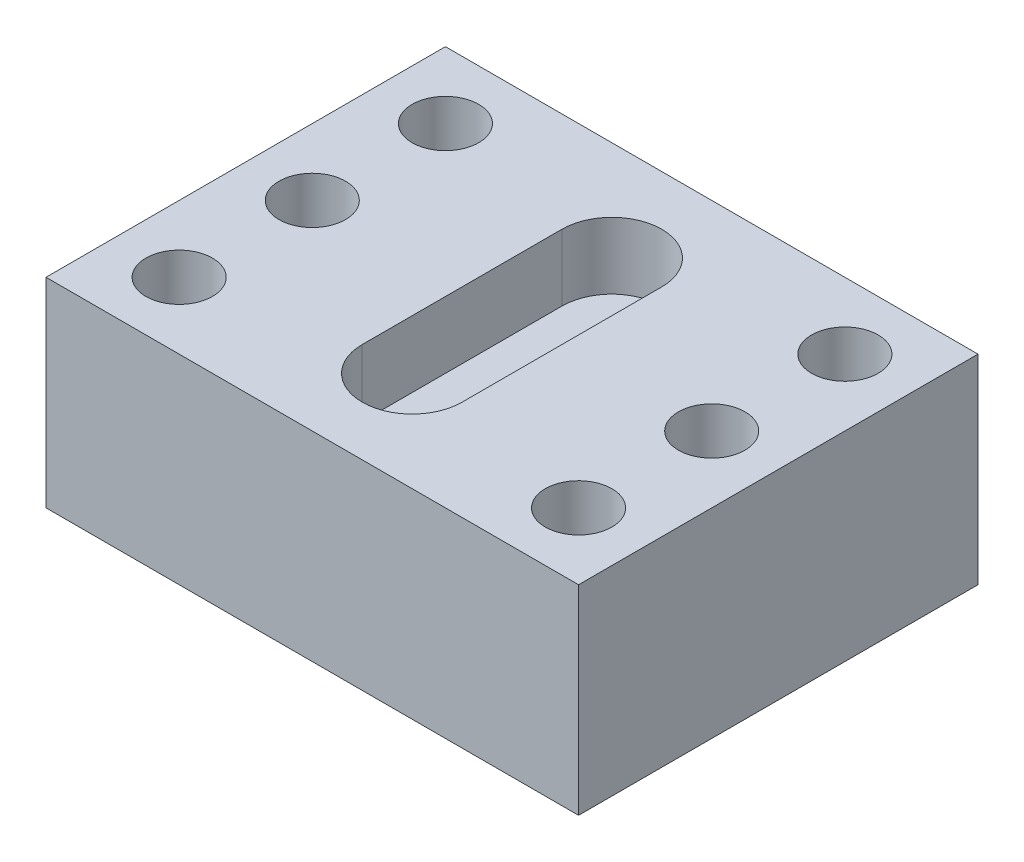
SolidWorks part; units mm, degrees
material "Plain Carbon Steel"
ref_plane "Front Plane" through (0, 0, 0) normal (0, 0, 1) x (1, 0, 0)
ref_plane "Top Plane" through (0, 0, 0) normal (0, 1, 0) x (1, 0, 0)
ref_plane "Right Plane" through (0, 0, 0) normal (1, 0, 0) x (0, 0, -1)
sketch "Sketch1" plane through (0, 0, 0) normal (0, 1, 0) x (1, 0, 0)
  line L1 (-101.6, -76.2) -> (101.6, -76.2)
  line L2 (-101.6, -76.2) -> (-101.6, 76.2)
  line L3 (-101.6, 76.2) -> (101.6, 76.2)
  line L4 (101.6, -76.2) -> (101.6, 76.2)
  line L5 (-101.6, -76.2) -> (101.6, 76.2) construction
  line L6 (-101.6, 76.2) -> (101.6, -76.2) construction
  point P0 (0, 0)
  dimension "D1" = 152.4
  dimension "D2" = 203.2
extrude "Boss-Extrude1" add sketch "Sketch1" along normal blind 76.2
sketch "Sketch2" plane through (0, 76.2, 0) normal (0, 1, 0) x (1, 0, 0)
  line L0 (-101.6, 76.2) -> (-101.6, -76.2) construction
  line L1 (-101.6, -76.2) -> (101.6, -76.2) construction
  line L2 (101.6, 76.2) -> (-101.6, 76.2) construction
  line L3 (0, 76.2) -> (0, -76.2) construction
  line L4 (-101.6, 0) -> (101.6, 0) construction
  line L6 (101.6, -76.2) -> (101.6, 76.2) construction
  line L9 (-19.05, -38.1) -> (-19.05, 38.1)
  line L11 (19.05, -38.1) -> (19.05, 38.1)
  circle A0 centre (-76.2, -50.8) radius 12.7
  circle A1 centre (-76.2, 0) radius 12.7
  circle A2 centre (-76.2, 50.8) radius 12.7
  circle A3 centre (76.2, 50.8) radius 12.7
  circle A4 centre (76.2, -50.8) radius 12.7
  circle A5 centre (76.2, 0) radius 12.7
  arc A6 (-19.05, -38.1) -> (19.05, -38.1) centre (0, -38.1) ccw
  arc A7 (-19.05, 38.1) -> (19.05, 38.1) centre (0, 38.1) cw
  point P23 (0, 0)
  dimension "D1" = 25.4
  dimension "D8" = 38.1
  dimension "D2" = 25.4
  dimension "D3" = 25.4
  dimension "D4" = 50.8
  dimension "D5" = 50.8
  dimension "D6" = 25.4
  dimension "D7" = 76.2
  dimension "D9" = 38.1
  dimension "D10" = 101.6
extrude "Cut-Extrude1" cut sketch "Sketch2" against normal blind 25.4
